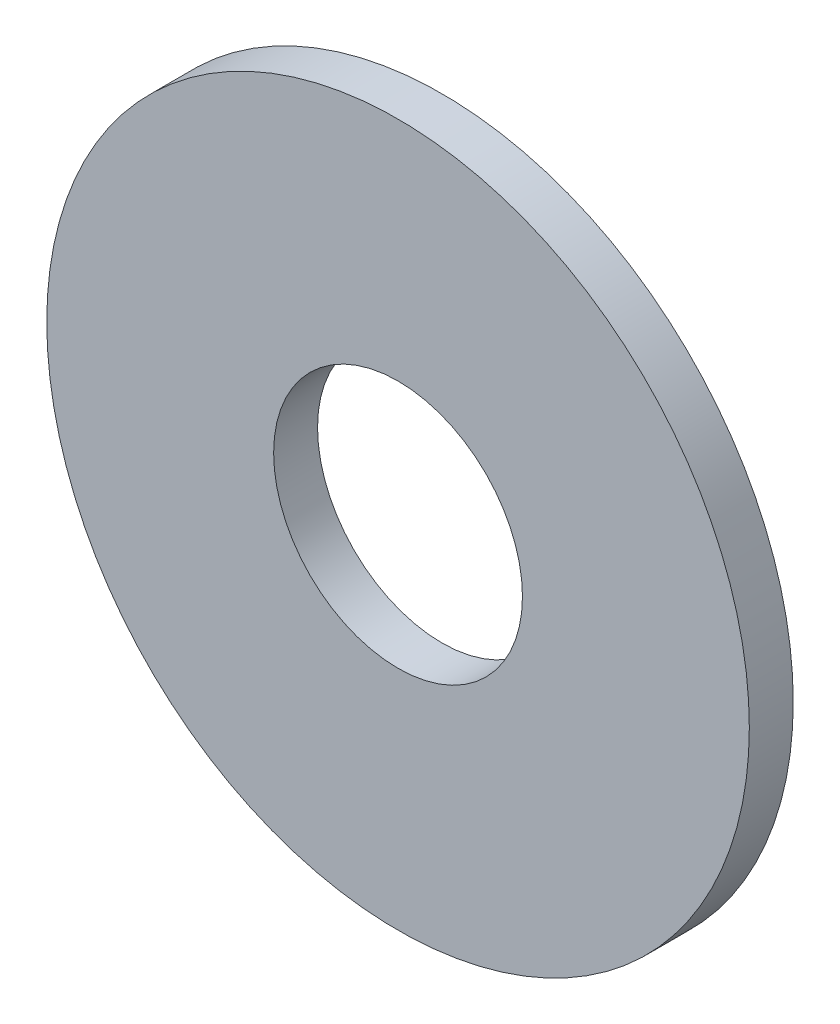
SolidWorks part; units mm, degrees
material "Сталь 45 ГОСТ 535-88"
ref_plane "Спереди" through (0, 0, 0) normal (0, 0, 1) x (1, 0, 0)
ref_plane "Сверху" through (0, 0, 0) normal (0, 1, 0) x (1, 0, 0)
ref_plane "Слева" through (0, 0, 0) normal (1, 0, 0) x (0, 0, -1)
sketch "Эскиз1" plane through (0, 0, 0) normal (0, 0, 1) x (1, 0, 0)
  circle A0 centre (0, 0) radius 8.5
  circle A1 centre (0, 0) radius 24
  dimension "D1" = 17
  dimension "D2" = 48
extrude "Вытянуть1" add sketch "Эскиз1" along normal blind 3
